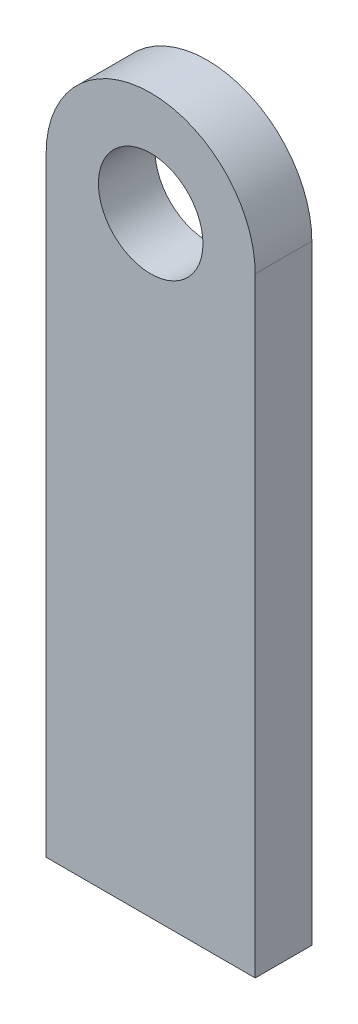
SolidWorks part; units mm, degrees
ref_plane "Płaszczyzna przednia" through (0, 0, 0) normal (0, 0, 1) x (1, 0, 0)
ref_plane "Płaszczyzna górna" through (0, 0, 0) normal (0, 1, 0) x (1, 0, 0)
ref_plane "Płaszczyzna prawa" through (0, 0, 0) normal (1, 0, 0) x (0, 0, -1)
sketch "Szkic1" plane through (0, 0, 0) normal (0, 0, 1) x (1, 0, 0)
  line L2 (-12, 0) -> (-12, -70)
  line L3 (-12, -70) -> (12, -70)
  line L4 (12, 0) -> (12, -70)
  arc A0 (12, 0) -> (-12, 0) centre (0, 0) ccw
  arc A1 (12, 0) -> (-12, 0) centre (0, 0) ccw
  circle A2 centre (0, 0) radius 6
  point P0 (0, 0)
  dimension "D1" = 12
  dimension "D3" = 12
  dimension "D2" = 70
extrude "Dodanie-wyciągnięcie1" add sketch "Szkic1" along normal blind 6.5 contours L4 A0 L2 L3 A2
